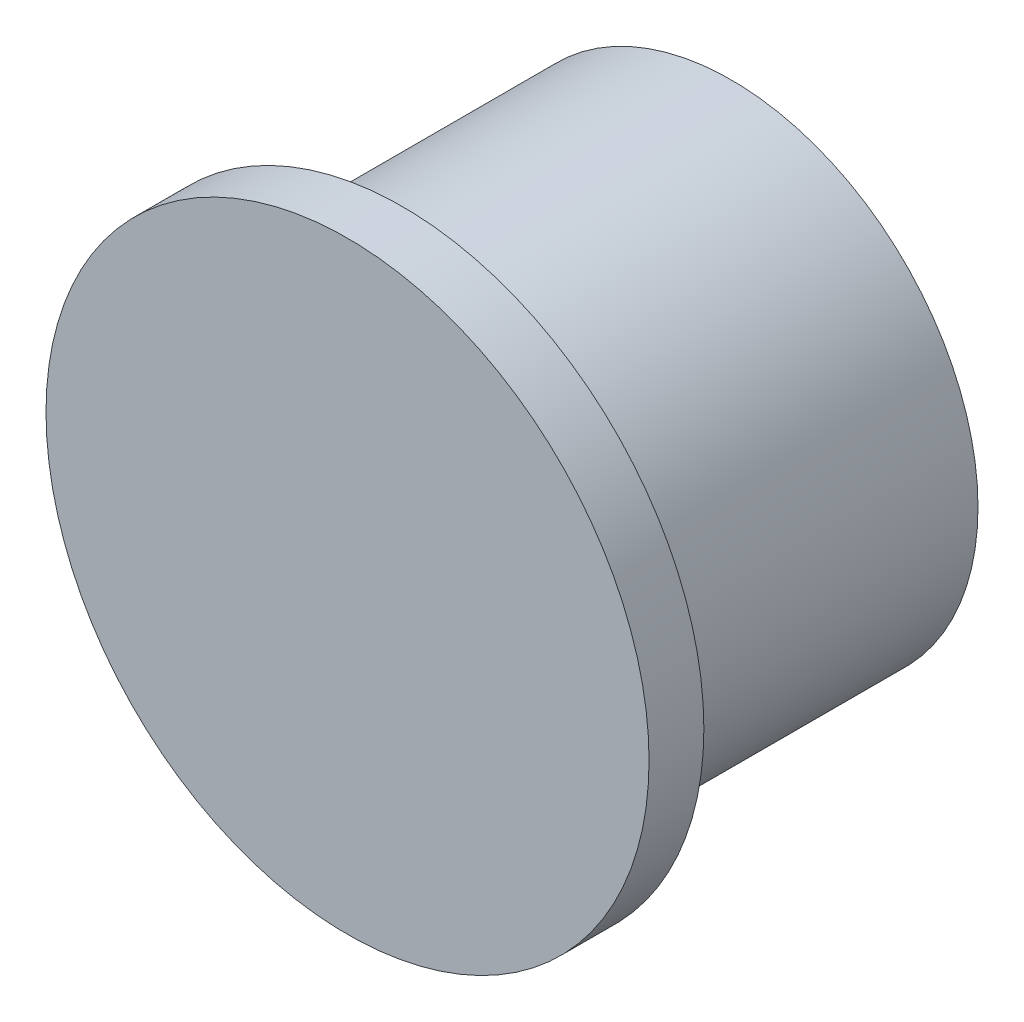
SolidWorks part; units mm, degrees
ref_plane "Front Plane" through (0, 0, 0) normal (0, 0, 1) x (1, 0, 0)
ref_plane "Top Plane" through (0, 0, 0) normal (0, 1, 0) x (1, 0, 0)
ref_plane "Right Plane" through (0, 0, 0) normal (1, 0, 0) x (0, 0, -1)
sketch "Sketch1" plane through (0, 0, 0) normal (0, 0, 1) x (1, 0, 0)
  circle A0 centre (0, 0) radius 11
  point P4 (0, 0)
  dimension "D1" = 22
extrude "Boss-Extrude1" add sketch "Sketch1" along normal blind 2
sketch "Sketch2" plane through (0, 0, 0) normal (0, 0, -1) x (-1, 0, 0)
  circle A0 centre (0, 0) radius 9
  dimension "D1" = 18
extrude "Boss-Extrude2" add sketch "Sketch2" along normal blind 12
